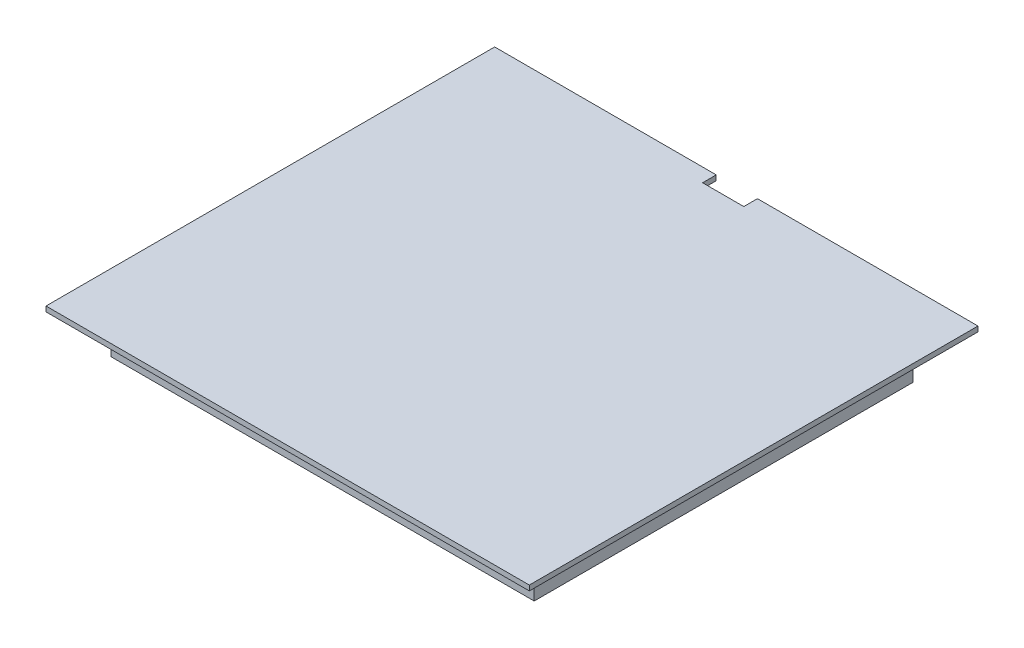
SolidWorks part; units mm, degrees
ref_plane "Front Plane" through (0, 0, 0) normal (0, 0, 1) x (1, 0, 0)
ref_plane "Top Plane" through (0, 0, 0) normal (0, 1, 0) x (1, 0, 0)
ref_plane "Right Plane" through (0, 0, 0) normal (1, 0, 0) x (0, 0, -1)
sketch "Sketch1" plane through (0, 0, 0) normal (0, 1, 0) x (1, 0, 0)
  line L1 (37.211, -34.544) -> (-37.211, -34.544)
  line L2 (37.211, -34.544) -> (37.211, 34.544)
  line L3 (37.211, 34.544) -> (-37.211, 34.544)
  line L4 (-37.211, -34.544) -> (-37.211, 34.544)
  line L5 (37.211, -34.544) -> (-37.211, 34.544) construction
  line L6 (37.211, 34.544) -> (-37.211, -34.544) construction
  point P0 (0, 0)
  dimension "D1" = 74.422
  dimension "D2" = 69.088
extrude "Boss-Extrude1" add sketch "Sketch1" along normal blind 0.7874
sketch "Sketch2" plane through (0, 0, 0) normal (0, -1, 0) x (1, 0, 0)
  line L1 (32.5833, -29.1674) -> (-32.5833, -29.1674)
  line L2 (32.5833, -29.1674) -> (32.5833, 29.1674)
  line L3 (32.5833, 29.1674) -> (-32.5833, 29.1674)
  line L4 (-32.5833, -29.1674) -> (-32.5833, 29.1674)
  line L5 (32.5833, -29.1674) -> (-32.5833, 29.1674) construction
  line L6 (32.5833, 29.1674) -> (-32.5833, -29.1674) construction
  point P0 (0, 0)
extrude "Boss-Extrude2" add sketch "Sketch2" along normal blind 6.35 separate body
sketch "Sketch3" plane through (0, 0.7874, 0) normal (0, 1, 0) x (1, 0, 0)
  line L0 (37.211, 34.544) -> (-37.211, 34.544) construction
  line L1 (-3.0942, 34.544) -> (3.2503, 34.544)
  line L2 (-3.0942, 34.544) -> (-3.0942, 32.4401)
  line L3 (-3.0942, 32.4401) -> (3.2503, 32.4401)
  line L4 (3.2503, 34.544) -> (3.2503, 32.4401)
extrude "Cut-Extrude1" cut sketch "Sketch3" against normal blind 6.35
